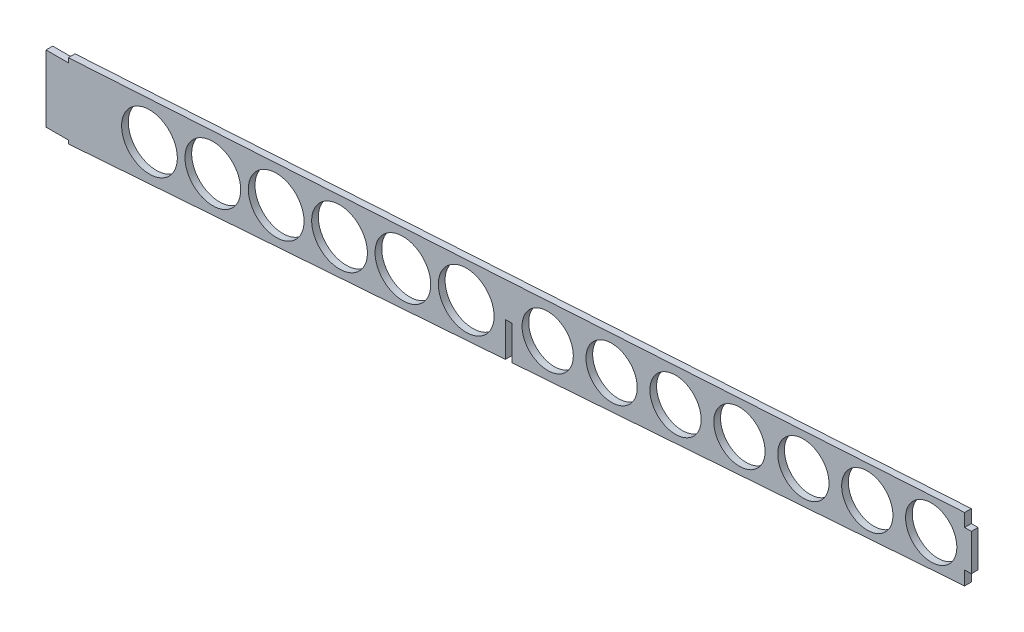
SolidWorks part; units mm, degrees
material "Pine"
ref_plane "Front Plane" through (0, 0, 0) normal (0, 0, 1) x (1, 0, 0)
ref_plane "Top Plane" through (0, 0, 0) normal (0, 1, 0) x (1, 0, 0)
ref_plane "Right Plane" through (0, 0, 0) normal (1, 0, 0) x (0, 0, -1)
sketch "Sketch1" plane through (0, 0, 0) normal (0, 0, 1) x (1, 0, 0)
  line L0 (-415, 15) -> (-405, 15) construction
  line L4 (-415, 1.5) -> (-415, 31.5)
  line L6 (-415, 31.5) -> (-405, 31.5)
  line L8 (-405, 0) -> (0, 0) construction
  line L9 (-415, 15) -> (0, 44.0196) construction
  line L10 (0, 58.0196) -> (0, 29.5196)
  line L11 (0, 44.0196) -> (0, 0) construction
  line L13 (-405, 0) -> (0, 29.5196)
  line L14 (-405, 31.5) -> (-405, 33.5)
  line L15 (-405, 33.5) -> (0, 58.0196)
  line L16 (-415, 1.5) -> (-405, 1.5)
  line L17 (-405, 1.5) -> (-405, 0)
  line L18 (-415, 1.5) -> (-415, 0) construction
  line L19 (-415, 0) -> (-405, 0) construction
  dimension "D1" = 415
  dimension "D2" = 10
  dimension "D3" = 33.5
  dimension "D4" = 4
  dimension "D5" = 28.5
  dimension "D6" = 14
  dimension "D8" = 2
  dimension "D9" = 15
  dimension "D10" = 30
extrude "Boss-Extrude1" add sketch "Sketch1" along normal blind 3
sketch "Sketch2" plane through (0, 0, 3) normal (0, 0, 1) x (1, 0, 0)
  line L0 (-415, 16.5) -> (-405, 16.5) construction
  line L1 (-415, 31.5) -> (-415, 1.5) construction
  line L2 (-405, 31.5) -> (-405, 16.5) construction
  line L6 (-207.5, 0) -> (-207.5, 29.8051) construction
  line L7 (-209, 29.8051) -> (-206, 29.8051)
  line L8 (-209, 29.8051) -> (-209, 14.286)
  line L9 (-405, 0) -> (0, 29.5196) construction
  line L10 (-209, 14.286) -> (-206, 14.286)
  line L11 (-206, 14.286) -> (-206, 29.8051)
  line L14 (-415, 0) -> (-415, 16.5) construction
  circle A1 centre (-397, 17.0389) radius 12.5 construction
  circle A2 centre (-368.5878, 18.953) radius 12.5
  circle A3 centre (-340.1756, 20.8671) radius 12.5
  circle A4 centre (-311.7634, 22.7811) radius 12.5
  circle A5 centre (-283.3512, 24.6952) radius 12.5
  circle A6 centre (-254.939, 26.6093) radius 12.5
  circle A7 centre (-226.5268, 28.5233) radius 12.5
  circle A11 centre (-190, 30.9841) radius 11.5
  circle A12 centre (-161.3313, 32.9154) radius 11.5
  circle A13 centre (-132.6625, 34.8467) radius 11.5
  circle A14 centre (-103.9938, 36.7781) radius 11.5
  circle A15 centre (-75.325, 38.7094) radius 11.5
  circle A16 centre (-46.6563, 40.6408) radius 11.5
  circle A17 centre (-17.9876, 42.5721) radius 11.5
  point P18 (-207.5, 29.8051)
  dimension "D3" = 25
  dimension "D6" = 23
  dimension "D1" = 3
  dimension "D2" = 18
  dimension "D7" = 16
  dimension "D4" = 7
  dimension "D8" = 7
other "AlignGroup1"
extrude "Cut-Extrude1" cut sketch "Sketch2" against normal through all both and the other way through all
sketch "Sketch3" plane through (0, 0, 3) normal (0, 0, 1) x (1, 0, 0)
  line L0 (0, 29.5196) -> (0, 58.0196) construction
  line L1 (0, 58.0196) -> (-3, 58.0196)
  line L2 (0, 58.0196) -> (0, 52.0196)
  line L3 (0, 52.0196) -> (-3, 52.0196)
  line L4 (-3, 58.0196) -> (-3, 52.0196)
  line L5 (0, 28.19) -> (-3, 28.19)
  line L6 (0, 28.19) -> (0, 35.5196)
  line L7 (0, 35.5196) -> (-3, 35.5196)
  line L8 (-3, 28.19) -> (-3, 35.5196)
  dimension "D1" = 3
  dimension "D2" = 6
  dimension "D3" = 6
extrude "Cut-Extrude2" cut sketch "Sketch3" against normal blind 10
